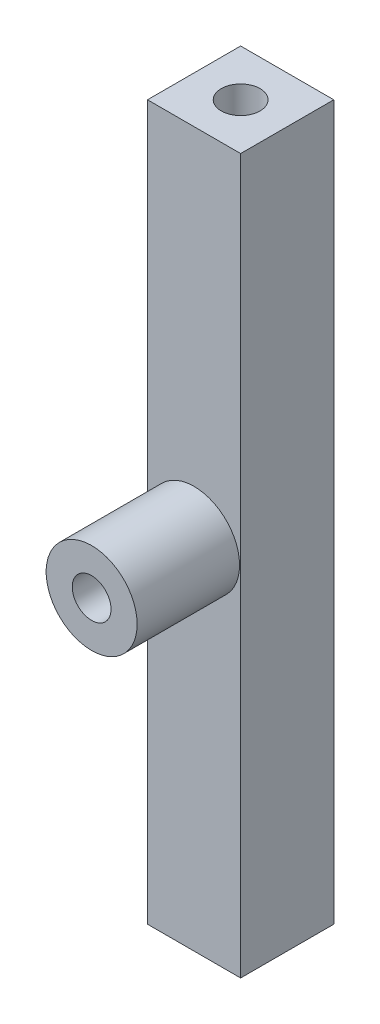
SolidWorks part; units mm, degrees
ref_plane "Front Plane" through (0, 0, 0) normal (0, 0, 1) x (1, 0, 0)
ref_plane "Top Plane" through (0, 0, 0) normal (0, 1, 0) x (1, 0, 0)
ref_plane "Right Plane" through (0, 0, 0) normal (1, 0, 0) x (0, 0, -1)
sketch "Sketch1" plane through (0, 0, 0) normal (0, 0, 1) x (1, 0, 0)
  line L1 (-3, 23) -> (3, 23)
  line L2 (-3, 23) -> (-3, -23)
  line L3 (-3, -23) -> (3, -23)
  line L4 (3, 23) -> (3, -23)
  line L5 (-3, 23) -> (3, -23) construction
  line L6 (-3, -23) -> (3, 23) construction
  point P0 (0, 0)
  dimension "D1" = 46
  dimension "D2" = 6
extrude "Boss-Extrude1" add sketch "Sketch1" along normal blind 6
sketch "Sketch2" plane through (0, 23, 0) normal (0, 1, 0) x (1, 0, 0)
  circle A0 centre (0, -3) radius 1.25
  circle A1 centre (0, -3) radius 1.25
  dimension "D1" = 2.5
sketch "Sketch3" plane through (0, -23, 0) normal (0, -1, 0) x (1, 0, 0)
  circle A0 centre (0, 3) radius 1.25
  dimension "D1" = 2.5
extrude "Cut-Extrude2" cut sketch "Sketch2" against normal blind 10 contours A0
extrude "Cut-Extrude3" cut sketch "Sketch3" against normal blind 10 contours A0
sketch "Sketch4" plane through (0, 0, 6) normal (0, 0, 1) x (1, 0, 0)
  line L0 (0, 23) -> (0, 0) construction
  line L1 (3, 23) -> (-3, 23) construction
  circle A0 centre (0, 0) radius 2.93
  dimension "D1" = 5.86
extrude "Boss-Extrude2" add sketch "Sketch4" along normal blind 6.6
sketch "Sketch5" plane through (0, 0, 12.6) normal (0, 0, 1) x (1, 0, 0)
  circle A0 centre (0, 0) radius 1.25
  dimension "D1" = 2.5
extrude "Cut-Extrude4" cut sketch "Sketch5" against normal blind 7
